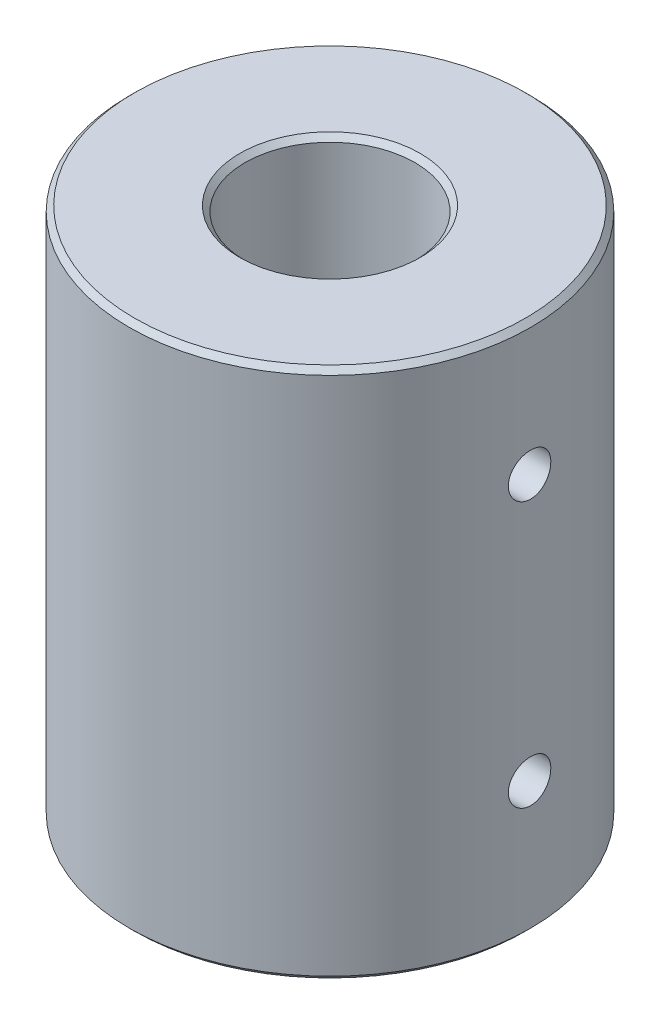
SolidWorks part; units mm, degrees
ref_plane "Front Plane" through (0, 0, 0) normal (0, 0, 1) x (1, 0, 0)
ref_plane "Top Plane" through (0, 0, 0) normal (0, 1, 0) x (1, 0, 0)
ref_plane "Right Plane" through (0, 0, 0) normal (1, 0, 0) x (0, 0, -1)
sketch "Sketch1" plane through (0, 0, 0) normal (0, 1, 0) x (1, 0, 0)
  circle A0 centre (0, 0) radius 9.45
  circle A1 centre (0, 0) radius 4
  dimension "D1" = 18.9
  dimension "D2" = 8
extrude "Boss-Extrude1" add sketch "Sketch1" along normal blind 25
sketch "Sketch2" plane through (0, 0, 0) normal (1, 0, 0) x (0, 0, -1)
  line L0 (9.45, 25) -> (-9.45, 25) construction
  line L1 (9.45, 25) -> (-9.45, 25)
  line L2 (-9.45, 0) -> (9.45, 0) construction
  line L3 (-9.45, 0) -> (9.45, 0)
  line L5 (0, 0) -> (0, 12.5)
  line L6 (0, 12.5) -> (0, 25)
  circle A0 centre (0, 6.25) radius 1
  circle A1 centre (0, 18.75) radius 1
extrude "Cut-Extrude1" cut sketch "Sketch2" against normal mid plane 25 contours A1 | A0
chamfer "Chamfer1" distance 0.25 angle 45 4 edges at (0, 25, 4) (0, 0, 4) (0, 0, 9.45) (0, 25, 9.45)
sketch "Sketch4" plane through (0, 0, 0) normal (1, 0, 0) x (0, 0, -1)
  line L0 (-9.45, 24.75) -> (9.45, 24.75) construction
  line L1 (-9.45, 0.25) -> (9.45, 0.25) construction
  line L2 (-9.45, 24.75) -> (9.45, 24.75) construction
  line L3 (-9.45, 0.25) -> (9.45, 0.25) construction
  line L4 (0, 24.75) -> (0, 0.25) construction
  point P6 (0, 12.5)
